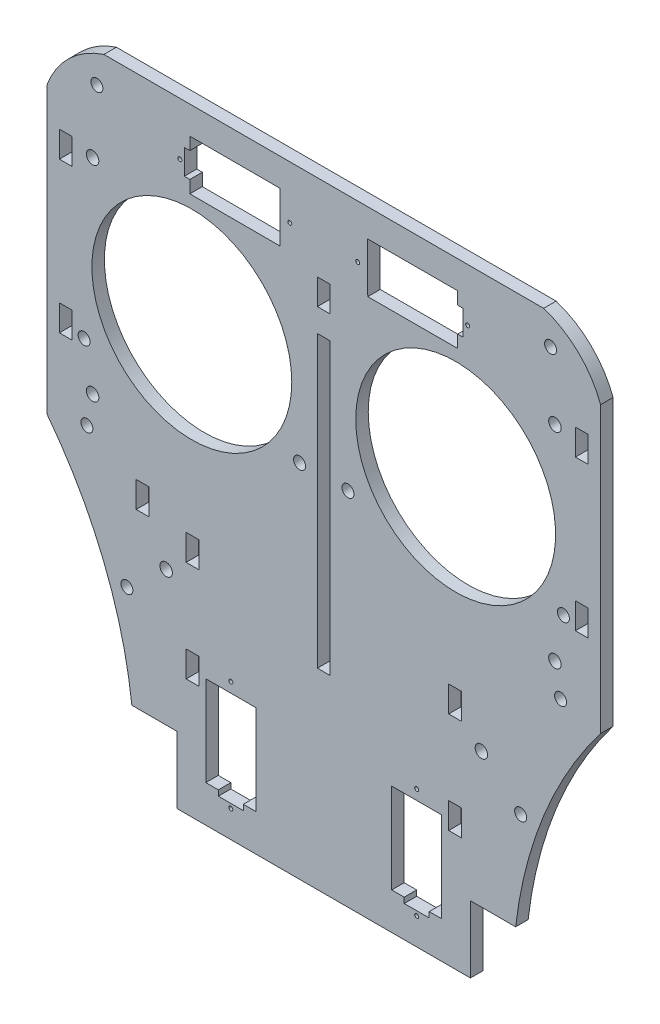
SolidWorks part; units mm, degrees
ref_plane "Front Plane" through (0, 0, 0) normal (0, 0, 1) x (1, 0, 0)
ref_plane "Top Plane" through (0, 0, 0) normal (0, 1, 0) x (1, 0, 0)
ref_plane "Right Plane" through (0, 0, 0) normal (1, 0, 0) x (0, 0, -1)
sketch "Sketch1" plane through (0, 0, 0) normal (0, 0, 1) x (1, 0, 0)
  line L0 (70.358, 0) -> (-70.358, 0)
  line L1 (-70.358, 0) -> (-70.358, -139.7)
  line L4 (-70.358, -139.7) -> (70.358, -139.7)
  line L5 (0, 0) -> (0, -139.7) construction
  line L8 (70.358, 0) -> (70.358, -139.7)
  dimension "D1" = 70.358
  dimension "D2" = 139.7
  dimension "D5" = 140.716
extrude "main body" add sketch "Sketch1" along normal blind 3.175
sketch "Sketch2" plane through (0, 0, 3.175) normal (0, 0, 1) x (1, 0, 0)
  line L0 (70.358, 0) -> (-70.358, 0) construction
  line L2 (-70.358, -139.7) -> (70.358, -139.7) construction
  line L3 (0, 0) -> (0, -139.7) construction
  circle A0 centre (-33.528, -48.26) radius 25.4
  circle A1 centre (-6.1468, -65.024) radius 1.524
  circle A2 centre (-60.9092, -65.024) radius 1.524
  point P71 (-52.324, -48.26)
  point P86 (-3.556, -48.26)
  point P87 (-3.556, -48.26)
  line B0 (-11.1701, -7.0861) -> (-34.0301, -7.0649)
  line B1 (-11.1819, -19.7861) -> (-11.1701, -7.0861)
  line B2 (-11.1819, -19.7861) -> (-34.0419, -19.7649)
  line B3 (-34.0419, -19.7649) -> (-34.0389, -16.5899)
  line B4 (-34.0389, -16.5899) -> (-35.4359, -16.5886)
  line B5 (-35.4359, -16.5886) -> (-35.4301, -10.2386)
  line B6 (-34.0331, -10.2399) -> (-35.4301, -10.2386)
  line B7 (-34.0331, -10.2399) -> (-34.0301, -7.0649)
  circle B8 centre (-36.576, -13.4125) radius 0.508
  circle B9 centre (-8.636, -13.4384) radius 0.508
  dimension "D3" = 33.528
  dimension "D8" = 54.7624
  dimension "D7" = 27.3812
  dimension "D4" = 3.048
  dimension "D5" = 3.048
  dimension "D6" = 48.26
  dimension "D2" = 50.8
  dimension "D1" = 27.94
sketch_block_instance "Block1-2"
sketch_block "Block1"
sketch_block_instance "servo_hole_SG90-1"
sketch_block "servo_hole_SG90" parameters "D5"=1.016, "D6"=1.016, "D9"=2.1092, "D1"=27.94, "D2"=6.35, "D3"=22.86, "D4"=12.7, "D7"=1.397, "D8"=6.35
extrude "cuts for eyes and motors" cut sketch "Sketch2" against normal through all
sketch "Sketch3" plane through (0, 0, 3.175) normal (0, 0, 1) x (1, 0, 0)
  line L4 (70.358, 0) -> (-70.358, 0) construction
  line L12 (0, -13.706) -> (0, -113.4305) construction
  line L20 (-63.9572, -66.929) -> (-67.183, -66.929)
  line L21 (-63.9572, -66.929) -> (-63.9572, -60.325)
  line L22 (-63.9572, -60.325) -> (-67.183, -60.325)
  line L23 (-67.183, -66.929) -> (-67.183, -60.325)
  line L24 (-63.9572, -66.929) -> (-67.183, -60.325) construction
  line L25 (-63.9572, -60.325) -> (-67.183, -66.929) construction
  line L29 (-65.6971, -22.098) -> (-65.6971, -28.702) construction
  line L32 (-67.183, -28.702) -> (-63.9572, -28.702)
  line L33 (-67.183, -28.702) -> (-67.183, -22.098)
  line L34 (-67.183, -22.098) -> (-63.9572, -22.098)
  line L35 (-63.9572, -28.702) -> (-63.9572, -22.098)
  line L36 (-67.183, -28.702) -> (-63.9572, -22.098) construction
  line L37 (-67.183, -22.098) -> (-63.9572, -28.702) construction
  line L44 (-70.358, 0) -> (-70.358, -139.7) construction
  dimension "D2" = 31.623
  dimension "D3" = 3.175
  dimension "D4" = 22.098
  dimension "D5" = 3.175
  dimension "D7" = 3.2258
  dimension "D12" = 3.2258
  dimension "D13" = 6.604
extrude "cut for assembly slots" cut sketch "Sketch3" against normal through all
sketch "Sketch4" plane through (0, 0, 3.175) normal (0, 0, 1) x (1, 0, 0)
  line L2 (0, -34.29) -> (0, -107.95) construction
  line L3 (-1.6129, -34.29) -> (1.6129, -34.29)
  line L4 (-1.6129, -34.29) -> (-1.6129, -107.95)
  line L5 (-1.6129, -107.95) -> (1.6129, -107.95)
  line L6 (1.6129, -34.29) -> (1.6129, -107.95)
  line L7 (70.358, 0) -> (-70.358, 0) construction
  line L9 (-1.6129, -28.3718) -> (1.6129, -28.3718)
  line L10 (-1.6129, -28.3718) -> (-1.6129, -21.844)
  line L11 (-1.6129, -21.844) -> (1.6129, -21.844)
  line L12 (1.6129, -28.3718) -> (1.6129, -21.844)
  line L13 (-1.6129, -28.3718) -> (1.6129, -21.844) construction
  line L14 (-1.6129, -21.844) -> (1.6129, -28.3718) construction
  point P13 (0, -25.1079)
  dimension "D1" = 3.2258
  dimension "D2" = 73.66
  dimension "D3" = 34.29
  dimension "D4" = 6.5278
  dimension "D5" = 3.2258
  dimension "D6" = 21.844
extrude "cut for nose" cut sketch "Sketch4" against normal through all
ref_plane "plane for eyelid mirror" through (0, 0, 0) normal (1, 0, 0) x (0, 0, -1)
sketch "Sketch9" plane through (0, 0, 3.175) normal (0, 0, 1) x (1, 0, 0)
  line L0 (-34.9758, -94.742) -> (-34.9758, -101.346)
  line L1 (-34.9758, -101.346) -> (-31.75, -101.346)
  line L2 (-31.75, -101.346) -> (-31.75, -94.742)
  line L3 (-31.75, -94.742) -> (-34.9758, -94.742)
  line L4 (-34.9758, -127) -> (-34.9758, -120.396)
  line L5 (-34.9758, -120.396) -> (-31.75, -120.396)
  line L6 (-31.75, -120.396) -> (-31.75, -127)
  line L7 (-31.75, -127) -> (-34.9758, -127)
  line L9 (0, -1.7463) -> (0, 1.7463) construction
  dimension "D1" = 3.2258
  dimension "D2" = 6.604
  dimension "D3" = 6.604
  dimension "D4" = 3.2258
  dimension "D5" = 12.7
  dimension "D6" = 19.05
  dimension "D7" = 31.75
extrude "slot for mandible" cut sketch "Sketch9" against normal through all
mirror "mirror of assembly slots" about plane through (0, 0, 0) normal (1, 0, 0) of "cut for assembly slots"
mirror "Mirror1" about plane through (0, 0, 0) normal (1, 0, 0) of "cuts for eyes and motors"
sketch "Sketch11" plane through (0, 0, 3.175) normal (0, 0, 1) x (1, 0, 0)
  line L0 (-70.358, -139.7) -> (-70.358, -86.36)
  line L1 (-70.358, 0) -> (-70.358, -139.7) construction
  line L4 (-70.358, 0) -> (-70.358, -13.97)
  line L5 (-70.358, 0) -> (-55.88, 0)
  line L6 (70.358, 0) -> (-70.358, 0) construction
  line L8 (-70.358, -139.7) -> (70.358, -139.7) construction
  line L9 (-70.358, -139.7) -> (-48.768, -139.7)
  arc A0 (-70.358, -86.36) -> (-48.768, -139.7) centre (-156.0073, -152.067) cw
  arc A1 (-70.358, -13.97) -> (-55.88, 0) centre (-48.7264, -21.9009) cw
  dimension "D1" = 21.59
  dimension "D2" = 53.34
  dimension "D3" = 13.97
  dimension "D4" = 14.478
extrude "cut for rounded face features" cut sketch "Sketch11" against normal through all
mirror "Mirror2" about plane through (0, 0, 0) normal (1, 0, 0) of "cut for rounded face features"
sketch "Sketch12" plane through (0, 0, 3.175) normal (0, 0, 1) x (1, 0, 0)
  line L0 (-70.358, -13.97) -> (-70.358, -86.36) construction
  line L1 (55.88, 0) -> (-55.88, 0) construction
  circle A0 centre (-57.658, -7.62) radius 1.524
  circle A1 centre (-60.198, -83.82) radius 1.524
  circle A2 centre (-50.038, -114.3) radius 1.524
  dimension "D1" = 3.048
  dimension "D2" = 3.048
  dimension "D3" = 3.048
  dimension "D4" = 10.16
  dimension "D5" = 12.7
  dimension "D6" = 114.3
  dimension "D7" = 20.32
  dimension "D8" = 7.62
  dimension "D9" = 83.82
extrude "holes for spacers" cut sketch "Sketch12" against normal through all
mirror "Mirror3" about plane through (0, 0, 0) normal (1, 0, 0) of "holes for spacers"
mirror "Mirror4" about plane through (0, 0, 0) normal (1, 0, 0) of "slot for mandible"
sketch "Sketch13" plane through (0, 0, 3.175) normal (0, 0, 1) x (1, 0, 0)
  line L0 (63.9572, -28.702) -> (63.9572, -22.098) construction
  line L1 (55.88, 0) -> (-55.88, 0) construction
  line L2 (63.9572, -66.929) -> (63.9572, -60.325) construction
  circle A0 centre (58.7502, -24.13) radius 1.5875
  circle A1 centre (58.7502, -76.2) radius 1.5875
  dimension "D1" = 3.175
  dimension "D4" = 3.175
  dimension "D2" = 5.207
  dimension "D3" = 24.13
  dimension "D5" = 76.2
  dimension "D6" = 5.207
extrude "cut for face plate mount screw" cut sketch "Sketch13" against normal through all
mirror "Mirror5" about plane through (0, 0, 0) normal (1, 0, 0) of "cut for face plate mount screw"
sketch "Sketch15" plane through (0, 0, 3.175) normal (0, 0, 1) x (1, 0, 0)
  line L0 (0, -139.7) -> (-37.2796, -139.7)
  line L1 (-48.768, -139.7) -> (48.768, -139.7) construction
  line L2 (-37.2796, -139.7) -> (-37.2796, -156.6983)
  line L3 (-37.2796, -156.6983) -> (0, -156.6983)
  line L4 (0, -1.7463) -> (0, 1.7463) construction
  line L5 (0, -156.6983) -> (0, -139.7)
extrude "extension for lip motor" add sketch "Sketch15" against normal blind 3.175
mirror "mirror of extension for lip motor" about plane through (0, 0, 0) normal (1, 0, 0) of "extension for lip motor"
sketch "Sketch16" plane through (0, 0, 3.175) normal (0, 0, 1) x (1, 0, 0)
  line L0 (-48.768, -139.7) -> (-37.2796, -139.7) construction
  line L1 (0, -1.7463) -> (0, 1.7463) construction
  line B0 (-17.272, -124.46) -> (-29.972, -124.46)
  line B1 (-17.272, -124.46) -> (-17.272, -147.32)
  line B2 (-17.272, -147.32) -> (-20.447, -147.32)
  line B3 (-29.972, -124.46) -> (-29.972, -147.32)
  line B4 (-20.447, -147.32) -> (-20.447, -148.717)
  line B5 (-20.447, -148.717) -> (-26.797, -148.717)
  line B6 (-26.797, -147.32) -> (-26.797, -148.717)
  line B7 (-26.797, -147.32) -> (-29.972, -147.32)
  circle B8 centre (-23.622, -149.86) radius 0.508
  circle B9 centre (-23.622, -121.92) radius 0.508
  dimension "D1" = 23.622
  dimension "D2" = 3.81
sketch_block_instance "servo_hole_SG90-2"
extrude "cut for lip motor" cut sketch "Sketch16" against normal through all
mirror "mirror of lip motor" about plane through (0, 0, 0) normal (1, 0, 0) of "cut for lip motor"
sketch "Sketch18" plane through (0, 0, 3.175) normal (0, 0, 1) x (1, 0, 0)
  line L0 (-34.9758, -94.742) -> (-34.9758, -101.346) construction
  circle A0 centre (-40.0558, -105.41) radius 1.5875
  dimension "D1" = 3.175
  dimension "D2" = 5.08
  dimension "D3" = 19.05
extrude "cut for bracket screw" cut sketch "Sketch18" against normal through all
mirror "mirror of bracket screw" about plane through (0, 0, 0) normal (1, 0, 0) of "cut for bracket screw"
sketch "Sketch19" plane through (0, 0, 3.175) normal (0, 0, 1) x (1, 0, 0)
  line L3 (-47.676, -89.4403) -> (-44.4248, -89.4403)
  line L4 (-47.676, -89.4403) -> (-47.676, -96.0443)
  line L5 (-47.676, -96.0443) -> (-44.4248, -96.0443)
  line L6 (-44.4248, -89.4403) -> (-44.4248, -96.0443)
  line L7 (-47.676, -89.4403) -> (-44.4248, -96.0443) construction
  line L8 (-47.676, -96.0443) -> (-44.4248, -89.4403) construction
  point P0 (-46.0504, -92.7423)
  dimension "D1" = 6.604
  dimension "D2" = 3.2512
  dimension "D3" = 22.682
  dimension "D4" = 3.0803
extrude "cut for gear tab" cut sketch "Sketch19" against normal through all
